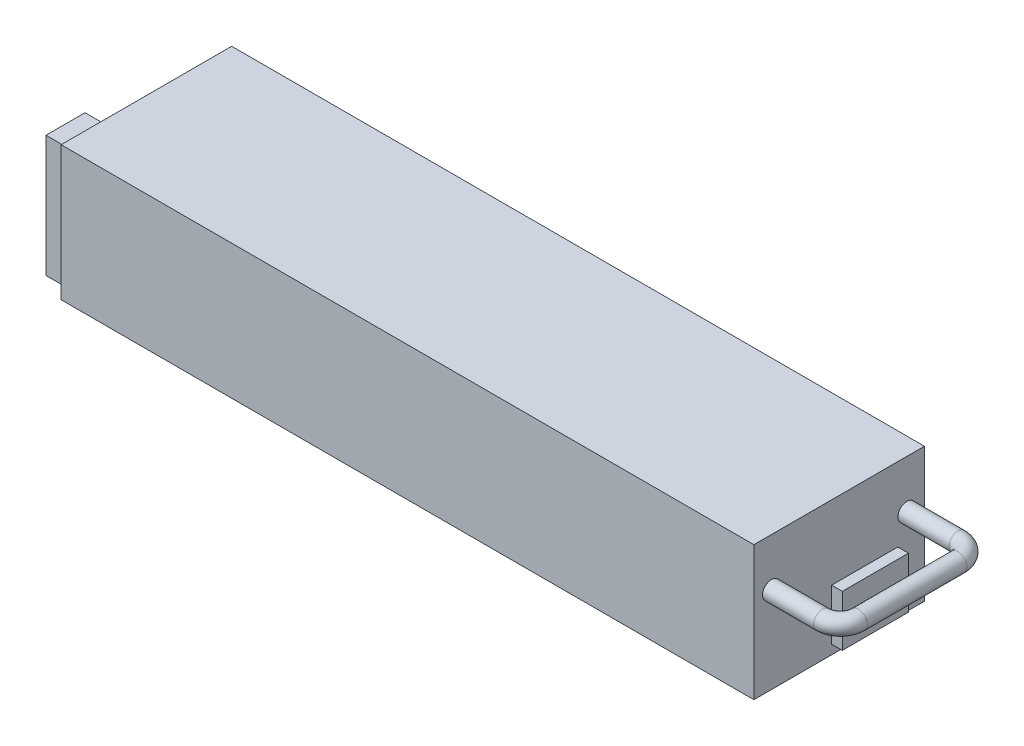
SolidWorks part; units mm, degrees
ref_plane "Front Plane" through (0, 0, 0) normal (0, 0, 1) x (1, 0, 0)
ref_plane "Top Plane" through (0, 0, 0) normal (0, 1, 0) x (1, 0, 0)
ref_plane "Right Plane" through (0, 0, 0) normal (1, 0, 0) x (0, 0, -1)
sketch "Sketch1" plane through (0, 0, 0) normal (0, 1, 0) x (1, 0, 0)
  line L1 (0, 0) -> (-325, 0)
  line L2 (0, 0) -> (0, -80)
  line L3 (0, -80) -> (-325, -80)
  line L4 (-325, 0) -> (-325, -80)
  dimension "D1" = 80
  dimension "D2" = 325
extrude "Boss-Extrude1" add sketch "Sketch1" along normal blind 63
sketch "Sketch2" plane through (0, 0, 0) normal (1, 0, 0) x (0, 0, -1)
  line L0 (-80, 63) -> (0, 63) construction
  line L1 (-71.75, 40.5) -> (-8.25, 40.5) construction
  line L2 (-40, 40.5) -> (-40, 63) construction
  circle A0 centre (-71.75, 40.5) radius 4.2
  circle A1 centre (-8.25, 40.5) radius 4.2
  dimension "D1" = 8.4
  dimension "D2" = 22.5
  dimension "D3" = 63.5
extrude "Boss-Extrude2" add sketch "Sketch2" along normal blind 24
sketch "Sketch3" plane through (24, 0, 0) normal (1, 0, 0) x (0, 0, -1)
  line L0 (-71.75, 40.5) -> (-63.35, 40.5) construction
  line L1 (-63.35, 40.5) -> (-8.25, 40.5) construction
  line L4 (-63.35, 40.5) -> (-63.35, 64.4234) construction
  circle A1 centre (-71.75, 40.5) radius 4.2
  circle A2 centre (-71.75, 40.5) radius 4.2
  dimension "D2" = 8.4
  dimension "D1" = 0
revolve "Revolve1" add sketch "Sketch3" angle 90 about L4
sketch "Sketch4" plane through (24, 0, 0) normal (1, 0, 0) x (0, 0, -1)
  line L0 (-8.25, 40.5) -> (-16.65, 40.5) construction
  line L1 (-16.65, 40.5) -> (-16.65, 62.5561) construction
  circle A2 centre (-8.25, 40.5) radius 4.2
  circle A3 centre (-8.25, 40.5) radius 4.2
  dimension "D2" = 8.4
  dimension "D1" = 0
revolve "Revolve2" add sketch "Sketch4" angle 90 about L1
sketch "Sketch5" plane through (0, 0, 16.65) normal (0, 0, 1) x (1, 0, 0)
  circle A1 centre (32.4, 40.5) radius 4.2
  circle A2 centre (32.4, 40.5) radius 4.2
  dimension "D1" = 0
extrude "Boss-Extrude3" add sketch "Sketch5" along normal up to surface (46.7 mm away) up to face at (28.2, 40.5, 63.35)
sketch "Sketch6" plane through (0, 0, 0) normal (1, 0, 0) x (0, 0, -1)
  line L0 (0, 63) -> (0, 0) construction
  line L1 (-43.5, 4.3) -> (-12.5, 4.3)
  line L2 (-43.5, 4.3) -> (-43.5, 28.3)
  line L3 (-43.5, 28.3) -> (-12.5, 28.3)
  line L4 (-12.5, 4.3) -> (-12.5, 28.3)
  line L5 (-80, 0) -> (0, 0) construction
  dimension "D1" = 31
  dimension "D2" = 24
  dimension "D3" = 12.5
  dimension "D4" = 4.3
extrude "Boss-Extrude4" add sketch "Sketch6" along normal blind 5
sketch "Sketch7" plane through (-325, 0, 0) normal (-1, 0, 0) x (0, 0, 1)
  line L0 (67.3395, 2.8) -> (67.3395, 0) construction
  line L1 (58.179, 59.8) -> (76.5, 59.8)
  line L2 (58.179, 59.8) -> (58.179, 2.8)
  line L3 (58.179, 2.8) -> (76.5, 2.8)
  line L4 (76.5, 59.8) -> (76.5, 2.8)
  line L5 (0, 0) -> (80, 0) construction
  line L6 (67.3395, 59.8) -> (67.3395, 63) construction
  line L7 (0, 63) -> (80, 63) construction
  line L8 (80, 63) -> (80, 0) construction
  dimension "D1" = 57
  dimension "D2" = 3.5
  dimension "D3" = 18.321
  dimension "D4" = 3.2
extrude "Boss-Extrude5" add sketch "Sketch7" along normal blind 10.6
sketch "Sketch8" plane through (0, 0, 0) normal (0, -1, 0) x (1, 0, 0)
  line L0 (-325, 80) -> (0, 80) construction
  line L1 (-325, 0) -> (-325, 80) construction
  line L2 (0, 80) -> (0, 0) construction
  circle A0 centre (-317, 65) radius 1.5
  circle A1 centre (-162.5, 74.5) radius 1.5
  circle A2 centre (-5.25, 55) radius 1.5
  dimension "D1" = 3
  dimension "D2" = 15
  dimension "D3" = 8
  dimension "D4" = 162.5
  dimension "D5" = 5.5
  dimension "D6" = 25
  dimension "D7" = 5.25
extrude "Cut-Extrude1" cut sketch "Sketch8" against normal blind 12
sketch "Sketch9" plane through (0, 0, 0) normal (0, 0, -1) x (-1, 0, 0)
  line L0 (0, 63) -> (0, 0) construction
  line L1 (0, 0) -> (325, 0) construction
  line L2 (0, 63) -> (325, 63) construction
  line L3 (325, 63) -> (325, 0) construction
  circle A0 centre (5.25, 26) radius 1.5
  circle A1 centre (297, 58) radius 1.5
  dimension "D3" = 3
  dimension "D6" = 3
  dimension "D1" = 5.25
  dimension "D2" = 26
  dimension "D4" = 5
  dimension "D5" = 28
extrude "Cut-Extrude3" cut sketch "Sketch9" against normal blind 12
